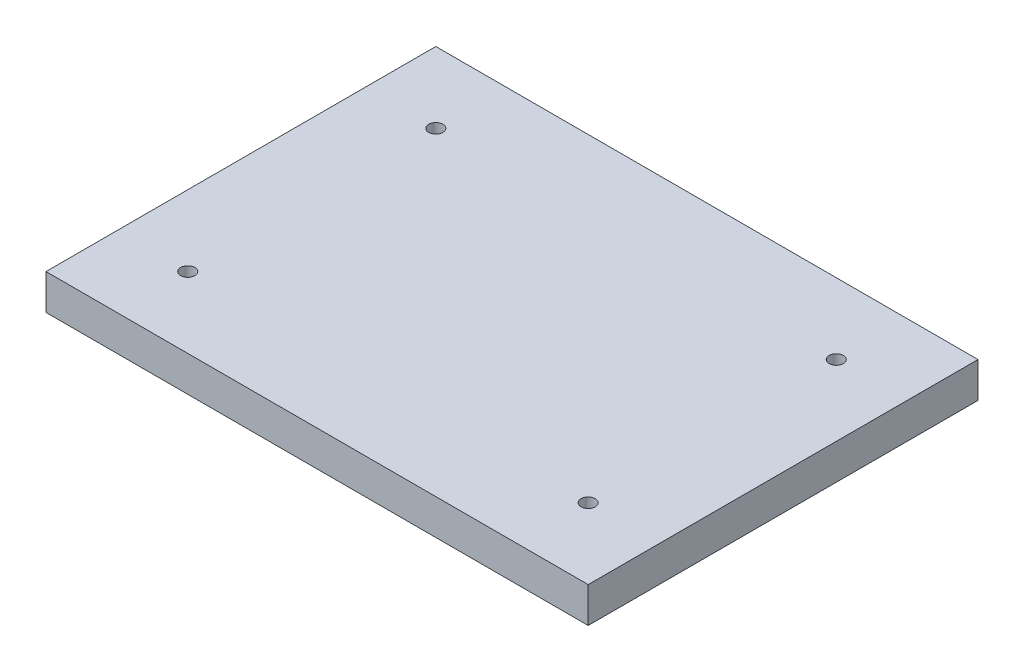
SolidWorks part; units mm, degrees
ref_plane "Front Plane" through (0, 0, 0) normal (0, 0, 1) x (1, 0, 0)
ref_plane "Top Plane" through (0, 0, 0) normal (0, 1, 0) x (1, 0, 0)
ref_plane "Right Plane" through (0, 0, 0) normal (1, 0, 0) x (0, 0, -1)
sketch "Sketch1" plane through (0, 0, 0) normal (0, 1, 0) x (1, 0, 0)
  line L22 (102, 15) -> (255, 15)
  line L23 (255, 15) -> (255, 125)
  line L26 (102, 125) -> (255, 125)
  line L30 (102, 125) -> (102, 15)
  circle A4 centre (122, 35) radius 2
  circle A5 centre (235, 35) radius 2
  circle A6 centre (235, 105) radius 2
  circle A7 centre (122, 105) radius 2
  point P0 (0, 0)
extrude "Boss-Extrude1" add sketch "Sketch1" along normal blind 10
